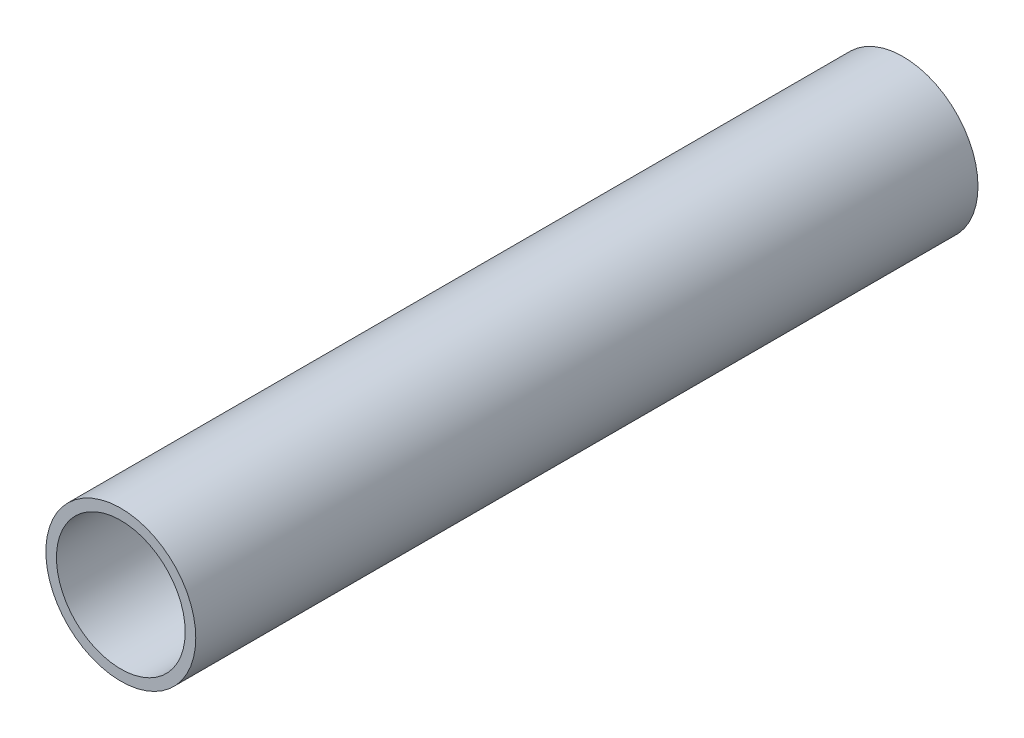
SolidWorks part; units mm, degrees
ref_plane "Front Plane" through (0, 0, 0) normal (0, 0, 1) x (1, 0, 0)
ref_plane "Top Plane" through (0, 0, 0) normal (0, 1, 0) x (1, 0, 0)
ref_plane "Right Plane" through (0, 0, 0) normal (1, 0, 0) x (0, 0, -1)
sketch "Sketch1" plane through (0, 0, 0) normal (0, 0, 1) x (1, 0, 0)
  circle A1 centre (0, 0) radius 36.5125
  circle A2 centre (0, 0) radius 31.3563
  dimension "D2" = 5.1562
  dimension "D1" = 73.025
extrude "Boss-Extrude1" add sketch "Sketch1" along normal blind 381
